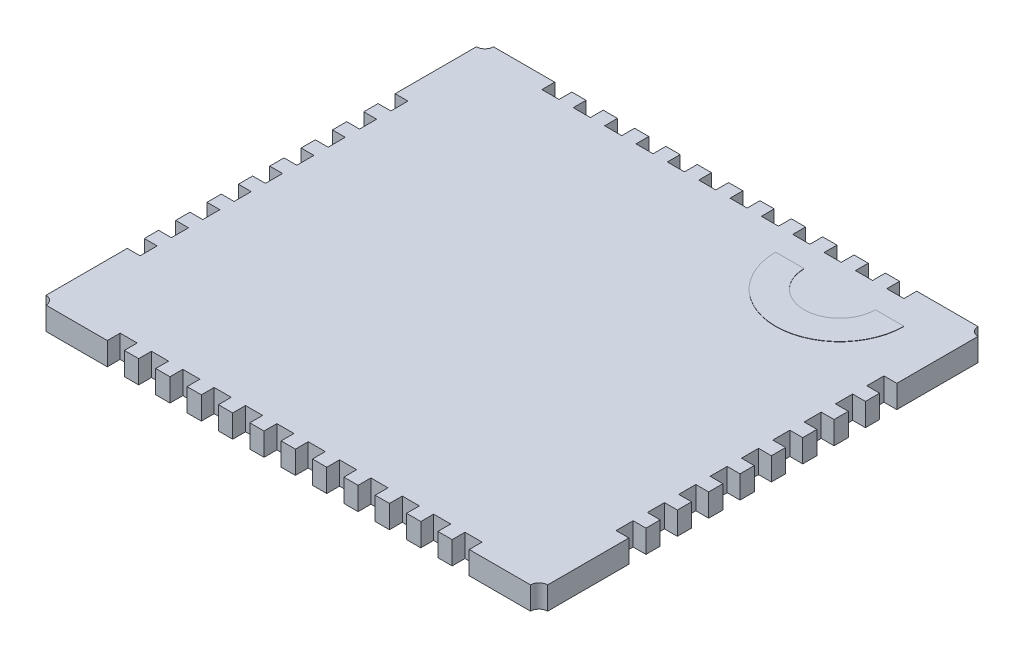
SolidWorks part; units mm, degrees
ref_plane "Plan de face" through (0, 0, 0) normal (0, 0, 1) x (1, 0, 0)
ref_plane "Plan de dessus" through (0, 0, 0) normal (0, 1, 0) x (1, 0, 0)
ref_plane "Plan de droite" through (0, 0, 0) normal (1, 0, 0) x (0, 0, -1)
sketch "Esquisse1" plane through (0, 0, 0) normal (0, 1, 0) x (1, 0, 0)
  line L0 (-8.8812, 3.9827) -> (-8.2812, 3.9827)
  line L1 (-12.1312, -11.2673) -> (-9.9812, -11.2673)
  line L2 (-12.4312, -10.9673) -> (-12.4312, -8.1173)
  line L3 (-12.1312, 4.4327) -> (-9.9812, 4.4327)
  line L4 (5.1688, -10.9673) -> (5.1688, -8.1173)
  line L5 (-12.4312, -11.2673) -> (5.1688, 4.4327) construction
  line L6 (-12.4312, 4.4327) -> (5.1688, -11.2673) construction
  line L7 (-8.2812, 4.4327) -> (-7.7812, 4.4327)
  line L8 (-9.9812, 4.4327) -> (-9.9812, 3.9827)
  line L9 (-9.9812, 3.9827) -> (-9.3812, 3.9827)
  line L10 (-9.3812, 4.4327) -> (-9.3812, 3.9827)
  line L11 (-12.4312, -0.4173) -> (-11.9812, -0.4173)
  line L12 (-12.4312, 0.6827) -> (-11.9812, 0.6827)
  line L13 (-8.8812, 4.4327) -> (-8.8812, 3.9827)
  line L14 (-8.2812, 4.4327) -> (-8.2812, 3.9827)
  line L15 (-7.7812, 3.9827) -> (-7.1812, 3.9827)
  line L16 (-7.7812, 4.4327) -> (-7.7812, 3.9827)
  line L17 (-7.1812, 4.4327) -> (-7.1812, 3.9827)
  line L18 (-6.6812, 3.9827) -> (-6.0812, 3.9827)
  line L19 (-6.6812, 4.4327) -> (-6.6812, 3.9827)
  line L20 (-6.0812, 4.4327) -> (-6.0812, 3.9827)
  line L21 (-5.5812, 3.9827) -> (-4.9812, 3.9827)
  line L22 (-5.5812, 4.4327) -> (-5.5812, 3.9827)
  line L23 (-4.9812, 4.4327) -> (-4.9812, 3.9827)
  line L24 (-4.4812, 3.9827) -> (-3.8812, 3.9827)
  line L25 (-4.4812, 4.4327) -> (-4.4812, 3.9827)
  line L26 (-3.8812, 4.4327) -> (-3.8812, 3.9827)
  line L27 (-3.3812, 3.9827) -> (-2.7812, 3.9827)
  line L28 (-3.3812, 4.4327) -> (-3.3812, 3.9827)
  line L29 (-2.7812, 4.4327) -> (-2.7812, 3.9827)
  line L30 (-2.2812, 3.9827) -> (-1.6812, 3.9827)
  line L31 (-2.2812, 4.4327) -> (-2.2812, 3.9827)
  line L32 (-1.6812, 4.4327) -> (-1.6812, 3.9827)
  line L33 (-1.1812, 3.9827) -> (-0.5812, 3.9827)
  line L34 (-1.1812, 4.4327) -> (-1.1812, 3.9827)
  line L35 (-0.5812, 4.4327) -> (-0.5812, 3.9827)
  line L36 (-0.0812, 3.9827) -> (0.5188, 3.9827)
  line L37 (-0.0812, 4.4327) -> (-0.0812, 3.9827)
  line L38 (0.5188, 4.4327) -> (0.5188, 3.9827)
  line L39 (1.0188, 3.9827) -> (1.6188, 3.9827)
  line L40 (1.0188, 4.4327) -> (1.0188, 3.9827)
  line L41 (1.6188, 4.4327) -> (1.6188, 3.9827)
  line L42 (2.1188, 3.9827) -> (2.7188, 3.9827)
  line L43 (2.1188, 4.4327) -> (2.1188, 3.9827)
  line L44 (2.7188, 4.4327) -> (2.7188, 3.9827)
  line L45 (-8.8812, -11.2673) -> (-8.8812, -10.8173)
  line L46 (-6.0812, -11.2673) -> (-5.5812, -11.2673)
  line L47 (-9.9812, -11.2673) -> (-9.9812, -10.8173)
  line L48 (-9.9812, -10.8173) -> (-9.3812, -10.8173)
  line L49 (-9.3812, -11.2673) -> (-9.3812, -10.8173)
  line L50 (-9.3812, 4.4327) -> (-8.8812, 4.4327)
  line L51 (-7.1812, 4.4327) -> (-6.6812, 4.4327)
  line L52 (-8.8812, -10.8173) -> (-8.2812, -10.8173)
  line L53 (-8.2812, -11.2673) -> (-8.2812, -10.8173)
  line L54 (-7.7812, -11.2673) -> (-7.7812, -10.8173)
  line L55 (-7.7812, -10.8173) -> (-7.1812, -10.8173)
  line L56 (-7.1812, -11.2673) -> (-7.1812, -10.8173)
  line L57 (-6.6812, -11.2673) -> (-6.6812, -10.8173)
  line L58 (-6.6812, -10.8173) -> (-6.0812, -10.8173)
  line L59 (-6.0812, -11.2673) -> (-6.0812, -10.8173)
  line L60 (-5.5812, -11.2673) -> (-5.5812, -10.8173)
  line L61 (-5.5812, -10.8173) -> (-4.9812, -10.8173)
  line L62 (-4.9812, -11.2673) -> (-4.9812, -10.8173)
  line L63 (-4.4812, -11.2673) -> (-4.4812, -10.8173)
  line L64 (-4.4812, -10.8173) -> (-3.8812, -10.8173)
  line L65 (-3.8812, -11.2673) -> (-3.8812, -10.8173)
  line L66 (-3.3812, -11.2673) -> (-3.3812, -10.8173)
  line L67 (-3.3812, -10.8173) -> (-2.7812, -10.8173)
  line L68 (-2.7812, -11.2673) -> (-2.7812, -10.8173)
  line L69 (-2.2812, -11.2673) -> (-2.2812, -10.8173)
  line L70 (-2.2812, -10.8173) -> (-1.6812, -10.8173)
  line L71 (-1.6812, -11.2673) -> (-1.6812, -10.8173)
  line L72 (-1.1812, -11.2673) -> (-1.1812, -10.8173)
  line L73 (-1.1812, -10.8173) -> (-0.5812, -10.8173)
  line L74 (-0.5812, -11.2673) -> (-0.5812, -10.8173)
  line L75 (-0.0812, -11.2673) -> (-0.0812, -10.8173)
  line L76 (-0.0812, -10.8173) -> (0.5188, -10.8173)
  line L77 (0.5188, -11.2673) -> (0.5188, -10.8173)
  line L78 (1.0188, -11.2673) -> (1.0188, -10.8173)
  line L79 (1.0188, -10.8173) -> (1.6188, -10.8173)
  line L80 (1.6188, -11.2673) -> (1.6188, -10.8173)
  line L81 (2.1188, -11.2673) -> (2.1188, -10.8173)
  line L82 (2.1188, -10.8173) -> (2.7188, -10.8173)
  line L83 (2.7188, -11.2673) -> (2.7188, -10.8173)
  line L84 (-8.2812, -11.2673) -> (-7.7812, -11.2673)
  line L85 (-7.1812, -11.2673) -> (-6.6812, -11.2673)
  line L86 (-9.3812, -11.2673) -> (-8.8812, -11.2673)
  line L87 (-4.9812, -11.2673) -> (-4.4812, -11.2673)
  line L88 (-3.8812, -11.2673) -> (-3.3812, -11.2673)
  line L89 (-2.7812, -11.2673) -> (-2.2812, -11.2673)
  line L90 (-1.6812, -11.2673) -> (-1.1812, -11.2673)
  line L91 (-0.5812, -11.2673) -> (-0.0812, -11.2673)
  line L92 (0.5188, -11.2673) -> (1.0188, -11.2673)
  line L93 (1.6188, -11.2673) -> (2.1188, -11.2673)
  line L94 (2.7188, -11.2673) -> (4.8688, -11.2673)
  line L95 (-6.0812, 4.4327) -> (-5.5812, 4.4327)
  line L96 (-4.9812, 4.4327) -> (-4.4812, 4.4327)
  line L97 (-3.8812, 4.4327) -> (-3.3812, 4.4327)
  line L98 (-2.7812, 4.4327) -> (-2.2812, 4.4327)
  line L99 (-1.6812, 4.4327) -> (-1.1812, 4.4327)
  line L100 (-0.5812, 4.4327) -> (-0.0812, 4.4327)
  line L101 (0.5188, 4.4327) -> (1.0188, 4.4327)
  line L102 (1.6188, 4.4327) -> (2.1188, 4.4327)
  line L103 (2.7188, 4.4327) -> (4.8688, 4.4327)
  line L104 (4.7188, -6.4173) -> (5.1688, -6.4173)
  line L105 (-12.4312, 1.2827) -> (-11.9812, 1.2827)
  line L106 (-11.9812, 0.6827) -> (-11.9812, 1.2827)
  line L107 (-12.4312, 0.6827) -> (-11.9812, 1.2827) construction
  line L108 (-12.4312, 1.2827) -> (-11.9812, 0.6827) construction
  line L109 (-11.9812, -0.4173) -> (-11.9812, 0.1827)
  line L110 (-12.4312, 0.1827) -> (-11.9812, 0.1827)
  line L111 (-12.4312, -1.5173) -> (-11.9812, -1.5173)
  line L112 (-11.9812, -1.5173) -> (-11.9812, -0.9173)
  line L113 (-12.4312, -0.9173) -> (-11.9812, -0.9173)
  line L114 (-12.4312, -2.6173) -> (-11.9812, -2.6173)
  line L115 (-11.9812, -2.6173) -> (-11.9812, -2.0173)
  line L116 (-12.4312, -2.0173) -> (-11.9812, -2.0173)
  line L117 (-12.4312, -3.7173) -> (-11.9812, -3.7173)
  line L118 (-11.9812, -3.7173) -> (-11.9812, -3.1173)
  line L119 (-12.4312, -3.1173) -> (-11.9812, -3.1173)
  line L120 (-12.4312, -4.8173) -> (-11.9812, -4.8173)
  line L121 (-11.9812, -4.8173) -> (-11.9812, -4.2173)
  line L122 (-12.4312, -4.2173) -> (-11.9812, -4.2173)
  line L123 (-12.4312, -5.9173) -> (-11.9812, -5.9173)
  line L124 (-11.9812, -5.9173) -> (-11.9812, -5.3173)
  line L125 (-12.4312, -5.3173) -> (-11.9812, -5.3173)
  line L126 (-12.4312, -7.0173) -> (-11.9812, -7.0173)
  line L127 (-11.9812, -7.0173) -> (-11.9812, -6.4173)
  line L128 (-12.4312, -6.4173) -> (-11.9812, -6.4173)
  line L129 (-12.4312, -8.1173) -> (-11.9812, -8.1173)
  line L130 (-11.9812, -8.1173) -> (-11.9812, -7.5173)
  line L131 (-12.4312, -7.5173) -> (-11.9812, -7.5173)
  line L132 (-12.4312, -7.5173) -> (-12.4312, -7.0173)
  line L133 (-12.4312, -6.4173) -> (-12.4312, -5.9173)
  line L134 (-12.4312, -5.3173) -> (-12.4312, -4.8173)
  line L135 (-12.4312, -4.2173) -> (-12.4312, -3.7173)
  line L136 (-12.4312, -3.1173) -> (-12.4312, -2.6173)
  line L137 (-12.4312, -2.0173) -> (-12.4312, -0.4173)
  line L138 (-12.4312, 0.1827) -> (-12.4312, 0.6827)
  line L139 (-12.4312, 1.2827) -> (-12.4312, 4.1327)
  line L140 (4.7188, -7.5173) -> (5.1688, -7.5173)
  line L141 (4.7188, -7.5173) -> (4.7188, -8.1173)
  line L142 (4.7188, -8.1173) -> (5.1688, -8.1173)
  line L143 (5.1688, -0.9173) -> (5.1688, -0.4173)
  line L144 (4.7188, -7.5173) -> (5.1688, -8.1173) construction
  line L145 (4.7188, -8.1173) -> (5.1688, -7.5173) construction
  line L146 (4.7188, -6.4173) -> (4.7188, -7.0173)
  line L147 (4.7188, -7.0173) -> (5.1688, -7.0173)
  line L148 (4.7188, -5.3173) -> (5.1688, -5.3173)
  line L149 (4.7188, -5.3173) -> (4.7188, -5.9173)
  line L150 (4.7188, -5.9173) -> (5.1688, -5.9173)
  line L151 (4.7188, -4.2173) -> (5.1688, -4.2173)
  line L152 (4.7188, -4.2173) -> (4.7188, -4.8173)
  line L153 (4.7188, -4.8173) -> (5.1688, -4.8173)
  line L154 (4.7188, -3.1173) -> (5.1688, -3.1173)
  line L155 (4.7188, -3.1173) -> (4.7188, -3.7173)
  line L156 (4.7188, -3.7173) -> (5.1688, -3.7173)
  line L157 (4.7188, -2.0173) -> (5.1688, -2.0173)
  line L158 (4.7188, -2.0173) -> (4.7188, -2.6173)
  line L159 (4.7188, -2.6173) -> (5.1688, -2.6173)
  line L160 (4.7188, -0.9173) -> (5.1688, -0.9173)
  line L161 (4.7188, -0.9173) -> (4.7188, -1.5173)
  line L162 (4.7188, -1.5173) -> (5.1688, -1.5173)
  line L163 (4.7188, 0.1827) -> (5.1688, 0.1827)
  line L164 (4.7188, 0.1827) -> (4.7188, -0.4173)
  line L165 (4.7188, -0.4173) -> (5.1688, -0.4173)
  line L166 (4.7188, 1.2827) -> (5.1688, 1.2827)
  line L167 (4.7188, 1.2827) -> (4.7188, 0.6827)
  line L168 (4.7188, 0.6827) -> (5.1688, 0.6827)
  line L169 (5.1688, -7.5173) -> (5.1688, -7.0173)
  line L170 (5.1688, -6.4173) -> (5.1688, -5.9173)
  line L171 (5.1688, -5.3173) -> (5.1688, -4.8173)
  line L172 (5.1688, -4.2173) -> (5.1688, -3.7173)
  line L173 (5.1688, -3.1173) -> (5.1688, -2.6173)
  line L174 (5.1688, -2.0173) -> (5.1688, -1.5173)
  line L175 (5.1688, 0.1827) -> (5.1688, 0.6827)
  line L176 (5.1688, 1.2827) -> (5.1688, 4.1327)
  arc A0 (-12.1312, -11.2673) -> (-12.4312, -10.9673) centre (-12.4312, -11.2673) ccw
  arc A1 (5.1688, -10.9673) -> (4.8688, -11.2673) centre (5.1688, -11.2673) ccw
  arc A2 (4.8688, 4.4327) -> (5.1688, 4.1327) centre (5.1688, 4.4327) ccw
  arc A3 (-12.4312, 4.1327) -> (-12.1312, 4.4327) centre (-12.4312, 4.4327) ccw
  point P0 (-3.6312, -3.4173)
  point P6 (-9.6812, 4.2077)
  point P18 (-9.6812, -11.0423)
  point P67 (-12.2062, 0.9827)
  point P116 (4.9438, -7.8173)
  dimension "D3" = 0.6
  dimension "D4" = 0.6
  dimension "D5" = 0.6
  dimension "D6" = 0.6
  dimension "D1" = 17.6
  dimension "D2" = 15.7
  dimension "D7" = 0.6
  dimension "D8" = 0.45
  dimension "D9" = 2.75
  dimension "D10" = 12
  dimension "D11" = 0.6
  dimension "D12" = 0.45
  dimension "D13" = 2.75
  dimension "D15" = 0.6
  dimension "D16" = 0.45
  dimension "D17" = 3.45
  dimension "D19" = 0.6
  dimension "D20" = 0.45
  dimension "D21" = 3.15
  dimension "D14" = 12
  dimension "D18" = 9
  dimension "D22" = 9
extrude "Boss.-Extru.1" add sketch "Esquisse1" along normal blind 0.8 contours A3 L139 L105 L106 L12 L138 L110 L109 L11 L137 L113 L112 L111 L116 L115 L114 L136 L119 L118 L117 L135 L122 L121 L120 L134 L125 L124 L123 L133 L128 L127 L126 L132 L131 L130 L129 L2 A0 L1 L47 L48 L49 L86 L45 L52 L53 L84 L54 L55 L56
sketch "Esquisse2" plane through (0, 0.8, 0) normal (0, 1, 0) x (1, 0, 0)
  line L0 (-2.1272, 3.1327) -> (4.2541, 3.1327) construction
  line L1 (2.7188, 4.4327) -> (4.8688, 4.4327) construction
  line L2 (1.3188, 3.6385) -> (1.3188, 2.3028) construction
  line L3 (5.1688, 1.2827) -> (5.1688, 4.1327) construction
  line L4 (-0.9312, 3.1327) -> (0.0688, 3.1327)
  line L5 (2.5688, 3.1327) -> (3.5688, 3.1327)
  arc A0 (2.5688, 3.1327) -> (0.0688, 3.1327) centre (1.3188, 3.1327) cw
  arc A1 (3.5688, 3.1327) -> (-0.9312, 3.1327) centre (1.3188, 3.1327) cw
  dimension "D1" = 1.3
  dimension "D2" = 3.85
extrude "Boss.-Extru.2" add sketch "Esquisse2" along normal blind 0.01
